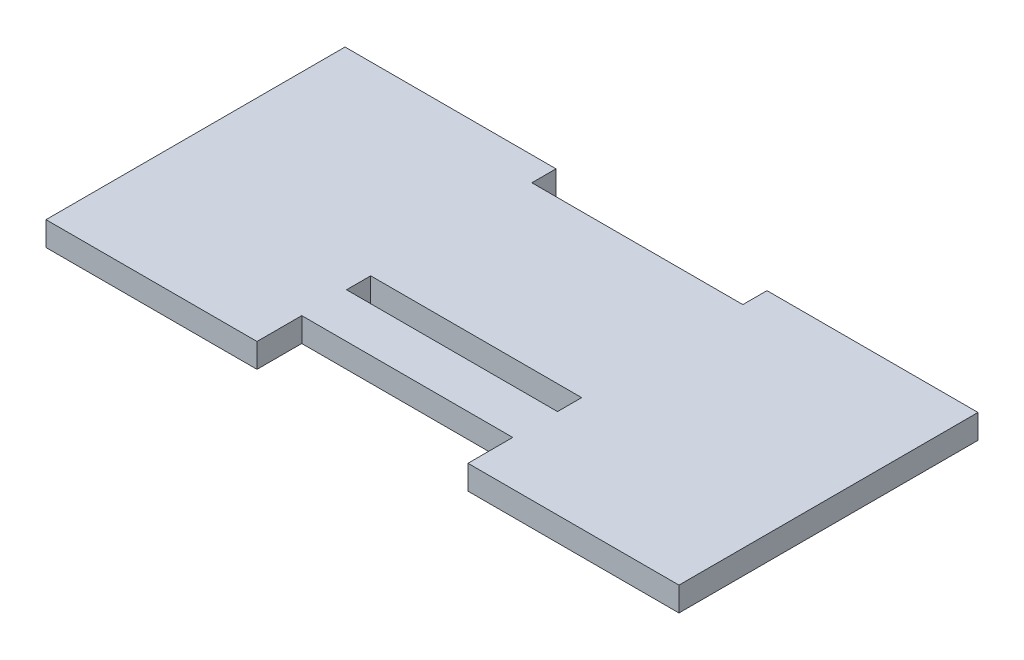
SolidWorks part; units mm, degrees
ref_plane "Front Plane" through (0, 0, 0) normal (0, 0, 1) x (1, 0, 0)
ref_plane "Top Plane" through (0, 0, 0) normal (0, 1, 0) x (1, 0, 0)
ref_plane "Right Plane" through (0, 0, 0) normal (1, 0, 0) x (0, 0, -1)
sketch "Sketch1" plane through (0, 0, 0) normal (0, 1, 0) x (1, 0, 0)
  line L0 (-34.5, -16.7) -> (-10.9333, -16.7)
  line L2 (-34.5, 16.7) -> (-34.5, -16.7)
  line L4 (36.2, 16.7) -> (36.2, -16.7)
  line L6 (-34.5, 16.7) -> (-10.9333, 16.7)
  line L9 (-10.9333, -6.7) -> (12.6333, -6.7)
  line L11 (-10.9333, 14) -> (12.6333, 14)
  line L13 (12.6333, 16.7) -> (36.2, 16.7)
  line L14 (-10.9333, -4) -> (12.6333, -4)
  line L15 (12.6333, -16.7) -> (36.2, -16.7)
  line L17 (-10.9333, -11.7) -> (12.6333, -11.7)
  line L20 (-10.9333, 16.7) -> (-10.9333, 14)
  line L22 (12.6333, 16.7) -> (12.6333, 14)
  line L23 (12.6333, -4) -> (12.6333, -6.7)
  line L24 (-10.9333, -4) -> (-10.9333, -6.7)
  line L25 (-10.9333, -11.7) -> (-10.9333, -16.7)
  line L26 (12.6333, -11.7) -> (12.6333, -16.7)
  point P0 (0, 0)
  dimension "D1" = 70.7
  dimension "D2" = 33.4
extrude "Boss-Extrude1" add sketch "Sketch1" along normal blind 2.7
